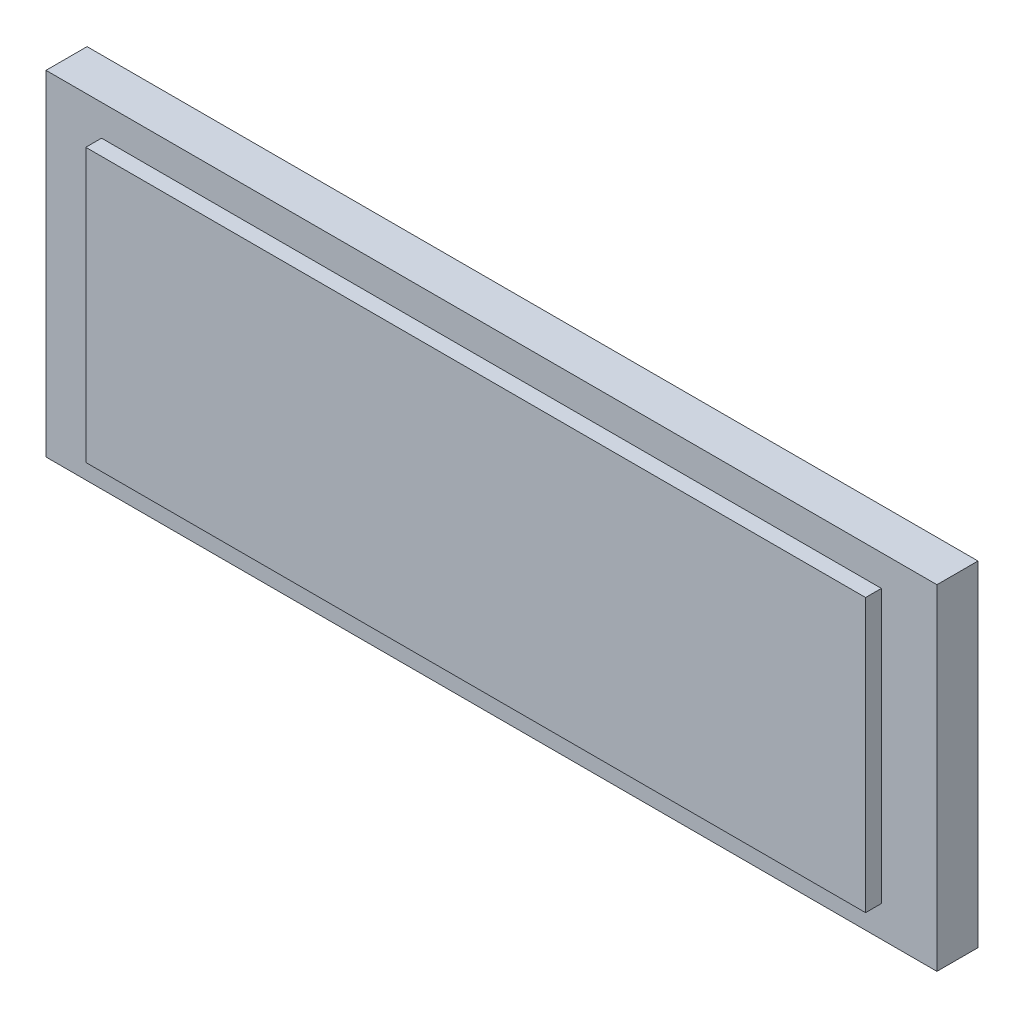
SolidWorks part; units mm, degrees
ref_plane "Front Plane" through (0, 0, 0) normal (0, 0, 1) x (1, 0, 0)
ref_plane "Top Plane" through (0, 0, 0) normal (0, 1, 0) x (1, 0, 0)
ref_plane "Right Plane" through (0, 0, 0) normal (1, 0, 0) x (0, 0, -1)
sketch "Sketch1" plane through (0, 0, 0) normal (0, 0, 1) x (1, 0, 0)
  line L1 (0, 0) -> (71.628, 0)
  line L2 (0, 0) -> (0, 26.924)
  line L3 (0, 26.924) -> (71.628, 26.924)
  line L4 (71.628, 0) -> (71.628, 26.924)
  dimension "D1" = 71.628
  dimension "D2" = 26.924
extrude "Boss-Extrude1" add sketch "Sketch1" along normal blind 3.302
sketch "Sketch2" plane through (0, 0, 3.302) normal (0, 0, 1) x (1, 0, 0)
  line L1 (4.4661, 24.4338) -> (67.1619, 24.4338)
  line L2 (4.4661, 24.4338) -> (4.4661, 2.4902)
  line L3 (4.4661, 2.4902) -> (67.1619, 2.4902)
  line L4 (67.1619, 24.4338) -> (67.1619, 2.4902)
  line L5 (4.4661, 24.4338) -> (67.1619, 2.4902) construction
  line L6 (4.4661, 2.4902) -> (67.1619, 24.4338) construction
  point P0 (35.814, 13.462)
extrude "Boss-Extrude2" add sketch "Sketch2" along normal blind 1.27
